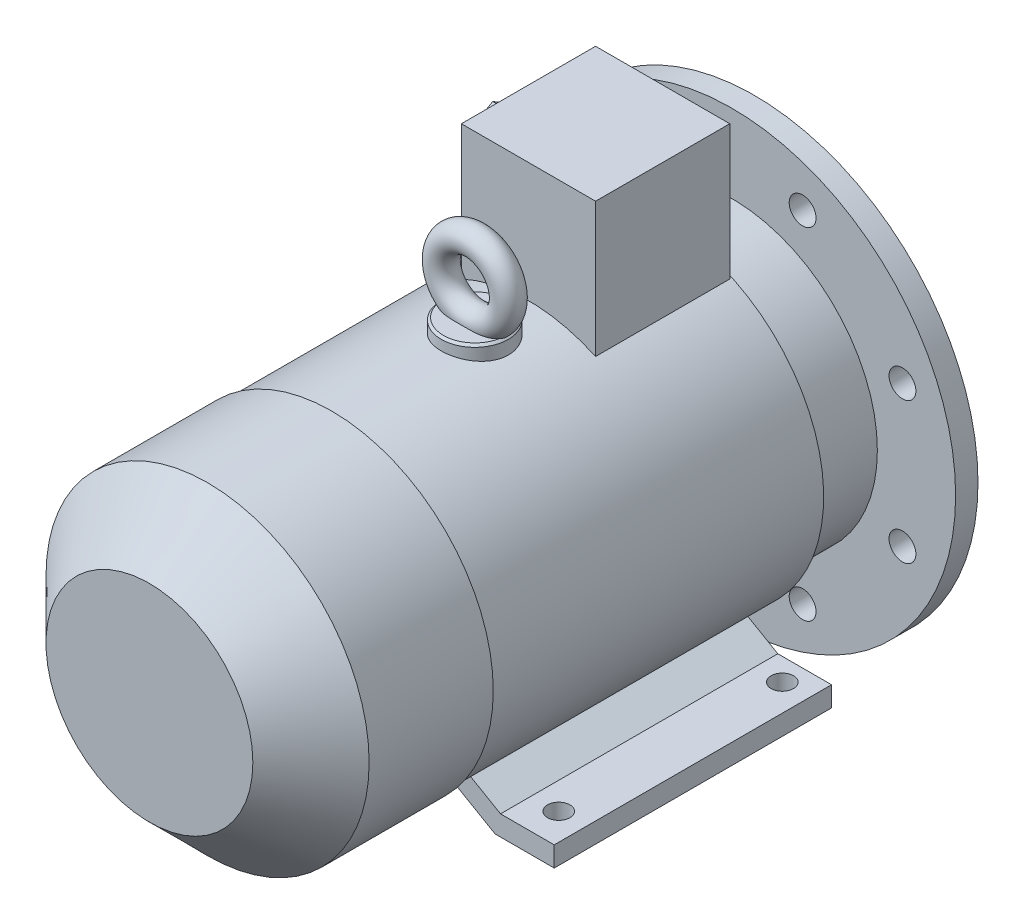
SolidWorks part; units mm, degrees
material "Ст.3 ГОСТ 380-88"
ref_plane "Спереди" through (0, 0, 0) normal (0, 0, 1) x (1, 0, 0)
ref_plane "Сверху" through (0, 0, 0) normal (0, 1, 0) x (1, 0, 0)
ref_plane "Справа" through (0, 0, 0) normal (1, 0, 0) x (0, 0, -1)
sketch "Эскиз1" plane through (0, 0, 0) normal (0, 0, 1) x (1, 0, 0)
  circle A0 centre (0, 0) radius 11
  dimension "D1" = 22
extrude "Вытянуть1" add sketch "Эскиз1" along normal blind 50
sketch "Эскиз2" plane through (0, 0, 0) normal (0, 0, -1) x (-1, 0, 0)
  line L0 (0, 0) -> (0, 12.6748) construction
  line L2 (-3, 13.5) -> (3, 13.5)
  line L3 (-3, 13.5) -> (-3, 7.5)
  line L4 (-3, 7.5) -> (3, 7.5)
  line L5 (3, 13.5) -> (3, 7.5)
  circle A1 centre (0, 0) radius 11 construction
  dimension "D1" = 6
  dimension "D2" = 6
  dimension "D3" = 24.5
extrude "Вытянуть2" add sketch "Эскиз2" against normal blind 25 and the other way blind 0.1
chamfer "Фаска1" distance 1 angle 45 1 edges at (0, -11, 0)
sketch "Эскиз3" plane through (0, 0, 50) normal (0, 0, 1) x (1, 0, 0)
  circle A0 centre (0, 0) radius 100
  dimension "D1" = 200
extrude "Вытянуть3" add sketch "Эскиз3" along normal blind 10
sketch "Эскиз4" plane through (0, 0, 50) normal (0, 0, -1) x (-1, 0, 0)
  circle A0 centre (0, 0) radius 65
  circle A1 centre (0, 0) radius 60
  dimension "D1" = 130
  dimension "D2" = 120
extrude "Вытянуть4" add sketch "Эскиз4" along normal blind 3.5
sketch "Эскиз5" plane through (0, 0, 50) normal (0, 0, -1) x (-1, 0, 0)
  circle A0 centre (0, 0) radius 60
  circle A1 centre (0, 0) radius 18
  dimension "D1" = 120
  dimension "D2" = 36
extrude "Вырез-Вытянуть1" cut sketch "Эскиз5" against normal blind 3.5
chamfer "Фаска2" distance 1 angle 45 2 edges at (-65, 0, 46.5) (-18, 0, 50)
sketch "Эскиз6" plane through (0, 0, 60) normal (0, 0, 1) x (1, 0, 0)
  circle A0 centre (0, 0) radius 65
  dimension "D1" = 130
extrude "Вытянуть5" add sketch "Эскиз6" along normal blind 30
sketch "Эскиз7" plane through (0, 0, 90) normal (0, 0, 1) x (1, 0, 0)
  circle A0 centre (0, 0) radius 71
  dimension "D1" = 142
extrude "Вытянуть6" add sketch "Эскиз7" along normal blind 149
sketch "Эскиз8" plane through (0, 0, 239) normal (0, 0, 1) x (1, 0, 0)
  circle A0 centre (0, 0) radius 72.2481
  dimension "D1" = 144.4962
extrude "Вытянуть7" add sketch "Эскиз8" along normal blind 81.5
chamfer "Фаска3" distance 26 angle 45 1 edges at (72.2481, 0, 320.5)
sketch "Эскиз9" plane through (0, 0, 50) normal (0, 0, -1) x (-1, 0, 0)
  line L0 (0, 0) -> (0, 120.2439) construction
  line L1 (0, 0) -> (-48.9872, 118.2656) construction
  circle A0 centre (-31.5714, 76.2201) radius 6
  circle A2 centre (31.5714, 76.2201) radius 6
  circle A3 centre (76.2201, 31.5714) radius 6
  circle A4 centre (76.2201, -31.5714) radius 6
  circle A5 centre (31.5714, -76.2201) radius 6
  circle A6 centre (-31.5714, -76.2201) radius 6
  circle A7 centre (-76.2201, -31.5714) radius 6
  circle A8 centre (-76.2201, 31.5714) radius 6
  dimension "D2" = 12
  dimension "D4" = 82.5
  dimension "D1" = 22.5
  dimension "D3" = 82.5
  dimension "D5" = 82.5
extrude "Вырез-Вытянуть2" cut sketch "Эскиз9" against normal through all
sketch "Эскиз10" plane through (0, 0, 90) normal (0, 0, -1) x (-1, 0, 0)
  line L0 (-74.5, -80) -> (-48.0885, -80)
  line L1 (-48.0885, -80) -> (-11.5155, -58.8846)
  line L2 (-11.5155, -58.8846) -> (-23.2951, -55.2932)
  line L3 (-23.2951, -55.2932) -> (-50.5, -71)
  line L4 (-50.5, -71) -> (-74.5, -71)
  line L5 (-74.5, -71) -> (-74.5, -80)
  line L6 (0, 0) -> (0, -117.9278) construction
  line L7 (74.5, -71) -> (74.5, -80)
  line L8 (50.5, -71) -> (74.5, -71)
  line L9 (74.5, -80) -> (48.0885, -80)
  line L10 (48.0885, -80) -> (11.5155, -58.8846)
  line L11 (11.5155, -58.8846) -> (23.2951, -55.2932)
  line L12 (23.2951, -55.2932) -> (50.5, -71)
  circle A0 centre (0, 0) radius 60 construction
  dimension "D1" = 9
  dimension "D2" = 74.5
  dimension "D3" = 24
  dimension "D4" = 9
  dimension "D5" = 60
  dimension "D6" = 80
extrude "Вытянуть8" add sketch "Эскиз10" against normal blind 124
sketch "Эскиз11" plane through (0, -80, 0) normal (0, -1, 0) x (1, 0, 0)
  line L0 (114.3491, 100) -> (-122.7539, 100) construction
  line L1 (0, 0) -> (0, 308.5542) construction
  line L2 (-62.5, 100) -> (62.5, 100) construction
  line L3 (-62.5, 100) -> (-62.5, 200) construction
  circle A0 centre (-62.5, 100) radius 5
  circle A1 centre (62.5, 100) radius 5
  circle A2 centre (-62.5, 200) radius 5
  circle A3 centre (62.5, 200) radius 5
  dimension "D2" = 10
  dimension "D1" = 100
  dimension "D3" = 62.5
  dimension "D4" = 90
  dimension "D5" = 200
  dimension "D6" = 100
  dimension "D7" = 125
extrude "Вырез-Вытянуть3" cut sketch "Эскиз11" against normal up to next
sketch "Эскиз12" plane through (0, 0, 0) normal (0, 1, 0) x (1, 0, 0)
  line L0 (0, 0) -> (0, -320.5) construction
  line L1 (-30, -91) -> (30, -91)
  line L2 (-30, -91) -> (-30, -151)
  line L3 (-30, -151) -> (30, -151)
  line L4 (30, -91) -> (30, -151)
  line L6 (-46.2481, -320.5) -> (46.2481, -320.5) construction
  line L8 (71, -90) -> (-71, -90) construction
  dimension "D1" = 60
  dimension "D2" = 1
  dimension "D3" = 60
extrude "Вытянуть9" add sketch "Эскиз12" along normal blind 124.5
sketch "Эскиз13" plane through (0, 0, 0) normal (0, 1, 0) x (1, 0, 0)
  line L0 (0, 0) -> (0, -239) construction
  line L1 (72.2481, -239) -> (-72.2481, -239) construction
  circle A0 centre (0, -175) radius 15
  dimension "D1" = 30
  dimension "D2" = 175
extrude "Вытянуть10" add sketch "Эскиз13" along normal blind 76.5
chamfer "Фаска4" distance 1 angle 45 1 edges at (0, 76.5, 190)
ref_plane "Плоскость1" through (0, 0, 175) normal (0, 0, 1) x (1, 0, 0)
sketch "Эскиз14" plane through (0, 0, 175) normal (0, 0, 1) x (1, 0, 0)
  line L0 (14, 76.5) -> (-14, 76.5) construction
  line L1 (0, 0) -> (0, 111.9091) construction
  line L2 (-70.1151, 113.5856) -> (-67.6125, 111.9091) construction
  circle A0 centre (0, 91.5) radius 15
  dimension "D1" = 30
sketch "Эскиз15" plane through (0, 0, 0) normal (1, 0, 0) x (0, 0, -1)
  line L1 (-175, 106.5) -> (-175, 76.5) construction
  circle A0 centre (-175, 106.5) radius 6
  dimension "D1" = 12
  dimension "D2" = 15
sweep "По траектории1" add profiles "Эскиз15" path "Эскиз14"
sketch "Эскиз16" plane through (-30, 0, 0) normal (-1, 0, 0) x (0, 0, 1)
  line L1 (91, 124.5) -> (91, 64.3506) construction
  line L2 (91, 124.5) -> (151, 124.5) construction
  circle A0 centre (121, 94.5) radius 8
  dimension "D1" = 16
  dimension "D2" = 30
  dimension "D3" = 30
extrude "Вытянуть11" add sketch "Эскиз16" along normal blind 6
sketch "Эскиз17" plane through (-36, 0, 0) normal (-1, 0, 0) x (0, 0, 1)
  line L1 (121, 110.0885) -> (107.5, 102.2942)
  line L2 (107.5, 102.2942) -> (107.5, 86.7058)
  line L3 (107.5, 86.7058) -> (121, 78.9115)
  line L4 (121, 78.9115) -> (134.5, 86.7058)
  line L5 (134.5, 86.7058) -> (134.5, 102.2942)
  line L6 (134.5, 102.2942) -> (121, 110.0885)
  line L7 (121, 94.5) -> (121, 137.7813) construction
  circle A0 centre (121, 94.5) radius 13.5 construction
  circle A1 centre (121, 94.5) radius 8 construction
  dimension "D1" = 27
extrude "Вытянуть12" add sketch "Эскиз17" along normal blind 10
sketch "Эскиз18" plane through (-46, 0, 0) normal (-1, 0, 0) x (0, 0, 1)
  circle A0 centre (121, 94.5) radius 6
  circle A1 centre (121, 94.5) radius 8 construction
  dimension "D1" = 12
extrude "Вырез-Вытянуть4" cut sketch "Эскиз18" against normal blind 10
